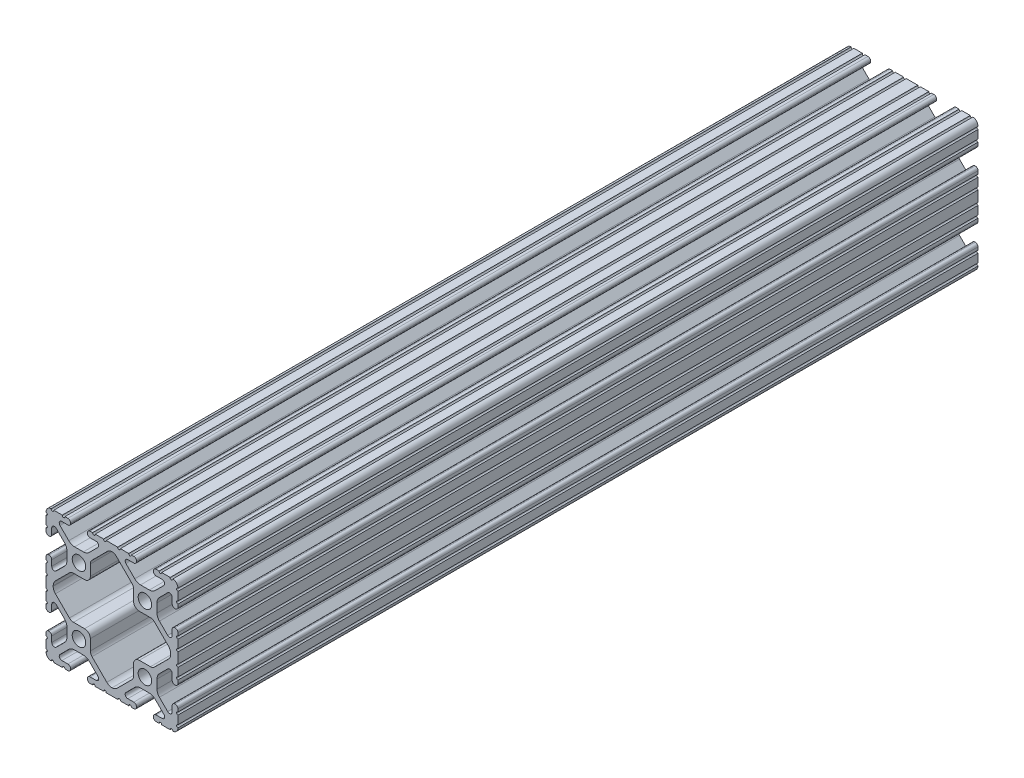
SolidWorks part; units mm, degrees
material "6061 Alloy"
ref_plane "Front Plane" through (0, 0, 0) normal (0, 0, 1) x (1, 0, 0)
ref_plane "Top Plane" through (0, 0, 0) normal (0, 1, 0) x (1, 0, 0)
ref_plane "Right Plane" through (0, 0, 0) normal (1, 0, 0) x (0, 0, -1)
sketch "Sketch1" plane through (0, 0, 0) normal (0, 0, 1) x (1, 0, 0)
  line L1 (-2.2101, -25.4) -> (2.2101, -25.4)
  line L2 (12.7883, 29.5847) -> (12.7883, -24.0404) construction
  line L3 (7.4579, -25.4) -> (8.4051, -25.4)
  line L4 (9.4615, -24.3587) -> (9.4615, -24.2315)
  line L5 (6.0878, -23.1902) -> (8.4051, -23.1902)
  line L6 (-12.7, -45.1098) -> (-12.7, 28.7522) construction
  line L7 (-25.8162, -12.7) -> (-12.7, -12.7) construction
  line L8 (0, 25.5922) -> (0, -25.5922) construction
  line L9 (-22.8238, 0) -> (0, 0) construction
  line L10 (8.763, -18.1257) -> (5.388, -21.5008)
  line L11 (14.3919, -17.1958) -> (11.0081, -17.1958)
  line L12 (20.012, -21.5008) -> (16.637, -18.1257)
  line L13 (16.9799, -23.1901) -> (19.2977, -23.1901)
  line L14 (15.9385, -24.3585) -> (15.9385, -24.2315)
  line L15 (16.9949, -25.4) -> (18.134, -25.4)
  line L16 (19.1384, -25.4) -> (20.1295, -25.4)
  line L17 (20.1295, -25.4) -> (22.4132, -25.4)
  line L18 (23.4501, -25.4) -> (23.4176, -25.4)
  line L19 (25.4, -23.294) -> (25.4, -23.2686)
  line L20 (25.4, -22.2526) -> (25.4, -21.1604)
  line L21 (25.4, -21.1604) -> (25.4, -19.0252)
  line L22 (25.4, -18.0092) -> (25.4, -16.916)
  line L23 (24.2316, -15.8746) -> (24.3586, -15.8746)
  line L24 (23.1902, -19.101) -> (23.1902, -16.916)
  line L25 (18.2781, -16.6418) -> (21.4558, -19.8194)
  line L26 (17.3482, -11.0035) -> (17.3482, -14.3967)
  line L27 (21.4566, -5.5875) -> (18.2808, -8.7557)
  line L28 (23.1902, -8.484) -> (23.1902, -6.3068)
  line L29 (-1.9878, -21.7759) -> (-7.684, -16.0797)
  line L30 (10.541, 8.1792) -> (14.8161, 8.1792)
  line L31 (-16.3772, -7.5334) -> (-21.7734, -2.1502)
  line L32 (24.3586, -9.5254) -> (24.2316, -9.5254)
  line L33 (25.4, -8.484) -> (25.4, -7.3277)
  line L34 (25.4, -3.0843) -> (25.4, -6.3117)
  line L35 (-25.4, 6.3117) -> (-25.4, 3.0843)
  line L36 (-22.6314, 0.0822) -> (-22.6314, -0.0822)
  line L37 (16.3772, -7.5334) -> (21.7734, -2.1502)
  line L38 (-14.8165, -8.1788) -> (-10.541, -8.1788)
  line L39 (12.7, -12.7) -> (25.8162, -12.7) construction
  line L40 (1.9878, -21.7759) -> (7.684, -16.0797)
  line L41 (3.2145, -25.4) -> (6.4535, -25.4)
  line L42 (22.6314, 0.0822) -> (22.6314, -0.0822)
  line L43 (-17.3482, -11.0035) -> (-17.3482, -14.3967)
  line L44 (25.4, 6.3117) -> (25.4, 3.0843)
  line L45 (-23.4501, -25.4) -> (-23.4176, -25.4)
  line L46 (-5.2705, 25.4) -> (-3.2145, 25.4)
  line L47 (-6.4535, 25.4) -> (-5.2705, 25.4)
  line L48 (-8.4051, 25.4) -> (-7.4579, 25.4)
  line L49 (-9.4615, 24.2315) -> (-9.4615, 24.3587)
  line L50 (-8.4051, 23.1902) -> (-6.0878, 23.1902)
  line L51 (-8.763, 18.1257) -> (-5.388, 21.5008)
  line L52 (-14.3919, 17.1958) -> (-11.0081, 17.1958)
  line L53 (-20.012, 21.5008) -> (-16.637, 18.1257)
  line L54 (-19.2977, 23.1901) -> (-16.9799, 23.1901)
  line L55 (-15.9385, 24.3585) -> (-15.9385, 24.2315)
  line L56 (-18.134, 25.4) -> (-16.9949, 25.4)
  line L57 (-20.1295, 25.4) -> (-19.1384, 25.4)
  line L58 (-22.4132, 25.4) -> (-20.1295, 25.4)
  line L59 (-23.4501, 25.4) -> (-23.4176, 25.4)
  line L60 (-25.4, 23.2686) -> (-25.4, 23.294)
  line L61 (-25.4, 21.1604) -> (-25.4, 22.2526)
  line L62 (-25.4, 19.0252) -> (-25.4, 21.1604)
  line L63 (-25.4, 16.916) -> (-25.4, 18.0092)
  line L64 (-24.3586, 15.8746) -> (-24.2316, 15.8746)
  line L65 (-23.1902, 19.101) -> (-23.1902, 16.916)
  line L66 (-18.2781, 16.6418) -> (-21.4558, 19.8194)
  line L67 (-17.3482, 11.0035) -> (-17.3482, 14.3967)
  line L68 (-21.4566, 5.5875) -> (-18.2808, 8.7557)
  line L69 (-23.1902, 6.3068) -> (-23.1902, 8.484)
  line L70 (-24.3586, 9.5254) -> (-24.2316, 9.5254)
  line L71 (-25.4, 7.3277) -> (-25.4, 8.484)
  line L74 (-14.8165, 8.1788) -> (-10.541, 8.1788)
  line L75 (-8.3312, 10.3886) -> (-8.3312, 14.5171)
  line L76 (3.2145, 25.4) -> (6.4535, 25.4)
  line L77 (1.7956, 21.9681) -> (7.684, 16.0797)
  line L78 (12.7, 12.7) -> (25.8162, 12.7) construction
  line L80 (16.3768, 7.5339) -> (21.7734, 2.1502)
  line L82 (25.4, 2.0683) -> (25.4, -2.0683)
  line L83 (8.3312, 12.7001) -> (8.3312, 10.389)
  line L84 (25.4, 7.3277) -> (25.4, 8.484)
  line L85 (24.3586, 9.5254) -> (24.2316, 9.5254)
  line L86 (-16.3772, 7.5334) -> (-21.7734, 2.1502)
  line L88 (-1.7956, 21.9681) -> (-7.684, 16.0797)
  line L89 (23.1902, 6.3068) -> (23.1902, 8.484)
  line L90 (21.4566, 5.5875) -> (18.2808, 8.7557)
  line L91 (17.3482, 11.0035) -> (17.3482, 14.3967)
  line L92 (18.2781, 16.6418) -> (21.4558, 19.8194)
  line L93 (23.1902, 19.101) -> (23.1902, 16.916)
  line L94 (24.2316, 15.8746) -> (24.3586, 15.8746)
  line L95 (25.4, 16.916) -> (25.4, 18.0092)
  line L96 (25.4, 19.0252) -> (25.4, 21.1604)
  line L97 (25.4, 21.1604) -> (25.4, 22.2526)
  line L98 (25.4, 23.2686) -> (25.4, 23.294)
  line L99 (23.4501, 25.4) -> (23.4176, 25.4)
  line L100 (20.1295, 25.4) -> (22.4132, 25.4)
  line L101 (19.1384, 25.4) -> (20.1295, 25.4)
  line L102 (16.9949, 25.4) -> (18.134, 25.4)
  line L103 (15.9385, 24.3585) -> (15.9385, 24.2315)
  line L104 (16.9799, 23.1901) -> (19.2977, 23.1901)
  line L105 (20.012, 21.5008) -> (16.637, 18.1257)
  line L106 (14.3919, 17.1958) -> (11.0081, 17.1958)
  line L107 (8.763, 18.1257) -> (5.388, 21.5008)
  line L108 (-25.8162, 12.7) -> (-12.7, 12.7) construction
  line L109 (6.0878, 23.1902) -> (8.4051, 23.1902)
  line L110 (9.4615, 24.2315) -> (9.4615, 24.3587)
  line L111 (7.4579, 25.4) -> (8.4051, 25.4)
  line L112 (8.3312, 12.7001) -> (8.3312, 14.5171)
  line L113 (-2.2101, 25.4) -> (2.2101, 25.4)
  line L114 (-22.4132, -25.4) -> (-20.1295, -25.4)
  line L115 (-20.1295, -25.4) -> (-19.1384, -25.4)
  line L116 (-18.134, -25.4) -> (-16.9949, -25.4)
  line L117 (-8.4051, -25.4) -> (-7.4579, -25.4)
  line L118 (-6.4535, -25.4) -> (-5.2705, -25.4)
  line L119 (-5.2705, -25.4) -> (-3.2145, -25.4)
  line L120 (-19.2977, -23.1901) -> (-16.9799, -23.1901)
  line L121 (-8.4051, -23.1902) -> (-6.0878, -23.1902)
  line L122 (-8.3312, -14.5171) -> (-8.3312, -10.3886)
  line L123 (-14.3919, -17.1958) -> (-11.0081, -17.1958)
  line L125 (-24.3586, -15.8746) -> (-24.2316, -15.8746)
  line L127 (-24.3586, -9.5254) -> (-24.2316, -9.5254)
  line L128 (14.8165, -8.1788) -> (10.541, -8.1788)
  line L129 (8.3312, -10.3886) -> (8.3312, -14.5171)
  line L130 (-9.4615, -24.3587) -> (-9.4615, -24.2315)
  line L132 (-15.9385, -24.3585) -> (-15.9385, -24.2315)
  line L134 (-25.4, -23.294) -> (-25.4, -23.2686)
  line L135 (-25.4, -22.2526) -> (-25.4, -21.1604)
  line L136 (-25.4, -21.1604) -> (-25.4, -19.0252)
  line L137 (-25.4, -18.0092) -> (-25.4, -16.916)
  line L138 (-25.4, -8.484) -> (-25.4, -7.3277)
  line L139 (-25.4, -6.3117) -> (-25.4, -4.1765)
  line L140 (-25.4, -4.1765) -> (-25.4, -3.0843)
  line L141 (-25.4, -2.0683) -> (-25.4, 2.0683)
  line L143 (-23.1902, -19.101) -> (-23.1902, -16.916)
  line L144 (-23.1902, -8.484) -> (-23.1902, -6.3068)
  line L198 (-21.4566, -5.5875) -> (-18.2808, -8.7557)
  line L200 (-18.2781, -16.6418) -> (-21.4558, -19.8194)
  line L213 (-20.012, -21.5008) -> (-16.637, -18.1257)
  line L215 (-8.763, -18.1257) -> (-5.388, -21.5008)
  arc A0 (6.4535, -25.4) -> (7.4579, -25.4) centre (6.9557, -25.3234) cw
  arc A1 (9.4615, -24.3587) -> (8.4051, -25.4) centre (8.4201, -24.3587) cw
  arc A2 (8.4051, -23.1902) -> (9.4615, -24.2315) centre (8.4201, -24.2315) cw
  arc A3 (6.0878, -23.1902) -> (5.388, -21.5008) centre (6.0878, -22.2006) cw
  arc A4 (8.763, -18.1257) -> (11.0081, -17.1958) centre (11.0081, -20.3708) cw
  arc A5 (14.3919, -17.1958) -> (16.637, -18.1257) centre (14.3919, -20.3708) cw
  arc A6 (20.012, -21.5008) -> (19.2977, -23.1901) centre (19.3122, -22.2006) cw
  arc A7 (15.9385, -24.2315) -> (16.9799, -23.1901) centre (16.9799, -24.2315) cw
  arc A8 (16.9949, -25.4) -> (15.9385, -24.3585) centre (16.9799, -24.3587) cw
  arc A9 (18.134, -25.4) -> (19.1384, -25.4) centre (18.6362, -25.3234) cw
  arc A10 (22.4132, -25.4) -> (23.4176, -25.4) centre (22.9154, -25.3234) cw
  arc A11 (25.4, -23.294) -> (23.4501, -25.4) centre (23.2918, -23.2977) cw
  arc A12 (25.4, -23.2686) -> (25.4, -22.2526) centre (25.4, -22.7606) cw
  arc A13 (25.4, -19.0252) -> (25.4, -18.0092) centre (25.4, -18.5172) cw
  arc A14 (24.3586, -15.8746) -> (25.4, -16.916) centre (24.3586, -16.916) cw
  arc A15 (23.1902, -16.916) -> (24.2316, -15.8746) centre (24.2316, -16.916) cw
  arc A16 (23.1902, -19.101) -> (21.4558, -19.8194) centre (22.1742, -19.101) cw
  arc A17 (18.2781, -16.6418) -> (17.3482, -14.3967) centre (20.5232, -14.3967) cw
  arc A18 (17.3482, -11.0035) -> (18.2808, -8.7557) centre (20.5232, -11.0035) cw
  arc A19 (0, -22.6304) -> (-1.9878, -21.7759) centre (0.0777, -19.7104) cw
  arc A20 (21.4566, -5.5875) -> (23.1902, -6.3068) centre (22.1742, -6.3068) cw
  arc A21 (24.2316, -9.5254) -> (23.1902, -8.484) centre (24.2316, -8.484) cw
  arc A22 (-14.8165, -8.1788) -> (-16.3772, -7.5334) centre (-14.8165, -5.969) cw
  arc A23 (-8.3312, -10.3886) -> (-10.541, -8.1788) centre (-10.541, -10.3886) ccw
  arc A24 (25.4, -8.484) -> (24.3586, -9.5254) centre (24.3586, -8.484) cw
  arc A25 (25.4, -7.3277) -> (25.4, -6.3117) centre (25.4, -6.8197) cw
  arc A26 (-22.6314, 0.0822) -> (-21.7734, 2.1502) centre (-19.7104, 0.0822) cw
  arc A27 (-7.684, -16.0797) -> (-8.3312, -14.5171) centre (-6.1214, -14.5171) cw
  arc A28 (-8.3312, 10.3886) -> (-10.541, 8.1788) centre (-10.541, 10.3886) cw
  circle A29 centre (12.7, -12.7) radius 2.6035
  arc A30 (14.8165, -8.1788) -> (16.3772, -7.5334) centre (14.8165, -5.969) ccw
  arc A31 (8.3312, -10.3886) -> (10.541, -8.1788) centre (10.541, -10.3886) cw
  arc A32 (8.3312, -14.5171) -> (7.684, -16.0797) centre (6.1214, -14.5171) cw
  arc A33 (0, -22.6304) -> (1.9878, -21.7759) centre (-0.0777, -19.7104) ccw
  arc A34 (2.2101, -25.4) -> (3.2145, -25.4) centre (2.7123, -25.3234) cw
  arc A35 (25.4, -3.0843) -> (25.4, -2.0683) centre (25.4, -2.5763) cw
  arc A36 (22.6314, 0.0822) -> (21.7734, 2.1502) centre (19.7104, 0.0822) ccw
  circle A37 centre (-12.7, -12.7) radius 2.6035
  arc A38 (-2.2101, 25.4) -> (-3.2145, 25.4) centre (-2.7123, 25.3234) cw
  arc A39 (-6.4535, 25.4) -> (-7.4579, 25.4) centre (-6.9557, 25.3234) cw
  arc A40 (-9.4615, 24.3587) -> (-8.4051, 25.4) centre (-8.4201, 24.3587) cw
  arc A41 (-8.4051, 23.1902) -> (-9.4615, 24.2315) centre (-8.4201, 24.2315) cw
  arc A42 (-6.0878, 23.1902) -> (-5.388, 21.5008) centre (-6.0878, 22.2006) cw
  arc A43 (-8.763, 18.1257) -> (-11.0081, 17.1958) centre (-11.0081, 20.3708) cw
  arc A44 (-14.3919, 17.1958) -> (-16.637, 18.1257) centre (-14.3919, 20.3708) cw
  arc A45 (-20.012, 21.5008) -> (-19.2977, 23.1901) centre (-19.3122, 22.2006) cw
  arc A46 (-15.9385, 24.2315) -> (-16.9799, 23.1901) centre (-16.9799, 24.2315) cw
  arc A47 (-16.9949, 25.4) -> (-15.9385, 24.3585) centre (-16.9799, 24.3587) cw
  arc A48 (-18.134, 25.4) -> (-19.1384, 25.4) centre (-18.6362, 25.3234) cw
  arc A49 (-22.4132, 25.4) -> (-23.4176, 25.4) centre (-22.9154, 25.3234) cw
  arc A50 (-25.4, 23.294) -> (-23.4501, 25.4) centre (-23.2918, 23.2977) cw
  arc A51 (-25.4, 23.2686) -> (-25.4, 22.2526) centre (-25.4, 22.7606) cw
  arc A52 (-25.4, 19.0252) -> (-25.4, 18.0092) centre (-25.4, 18.5172) cw
  arc A53 (-24.3586, 15.8746) -> (-25.4, 16.916) centre (-24.3586, 16.916) cw
  arc A54 (-23.1902, 16.916) -> (-24.2316, 15.8746) centre (-24.2316, 16.916) cw
  arc A55 (-23.1902, 19.101) -> (-21.4558, 19.8194) centre (-22.1742, 19.101) cw
  arc A56 (-18.2781, 16.6418) -> (-17.3482, 14.3967) centre (-20.5232, 14.3967) cw
  arc A57 (-17.3482, 11.0035) -> (-18.2808, 8.7557) centre (-20.5232, 11.0035) cw
  arc A58 (-21.4566, 5.5875) -> (-23.1902, 6.3068) centre (-22.1742, 6.3068) cw
  arc A59 (-24.2316, 9.5254) -> (-23.1902, 8.484) centre (-24.2316, 8.484) cw
  arc A60 (-25.4, 8.484) -> (-24.3586, 9.5254) centre (-24.3586, 8.484) cw
  arc A61 (-25.4, 7.3277) -> (-25.4, 6.3117) centre (-25.4, 6.8197) cw
  arc A62 (-25.4, 3.0843) -> (-25.4, 2.0683) centre (-25.4, 2.5763) cw
  circle A63 centre (-12.7, 12.7) radius 2.6035
  arc A64 (-8.3312, 14.5171) -> (-7.684, 16.0797) centre (-6.1214, 14.5171) cw
  arc A65 (2.2101, 25.4) -> (3.2145, 25.4) centre (2.7123, 25.3234) ccw
  arc A66 (0, 22.8111) -> (-1.7956, 21.9681) centre (0.2699, 19.9026) ccw
  arc A67 (8.3312, 14.5171) -> (7.684, 16.0797) centre (6.1214, 14.5171) ccw
  arc A68 (10.541, 8.1792) -> (8.3312, 10.389) centre (10.541, 10.389) cw
  arc A69 (14.8161, 8.1792) -> (16.3768, 7.5339) centre (14.8161, 5.9694) cw
  circle A70 centre (12.7, 12.7) radius 2.6035
  arc A71 (25.4, 3.0843) -> (25.4, 2.0683) centre (25.4, 2.5763) ccw
  arc A72 (-14.8165, 8.1788) -> (-16.3772, 7.5334) centre (-14.8165, 5.969) ccw
  arc A73 (25.4, 7.3277) -> (25.4, 6.3117) centre (25.4, 6.8197) ccw
  arc A74 (25.4, 8.484) -> (24.3586, 9.5254) centre (24.3586, 8.484) ccw
  arc A75 (22.6314, -0.0822) -> (21.7734, -2.1502) centre (19.7104, -0.0822) cw
  arc A76 (-22.6314, -0.0822) -> (-21.7734, -2.1502) centre (-19.7104, -0.0822) ccw
  arc A77 (24.2316, 9.5254) -> (23.1902, 8.484) centre (24.2316, 8.484) ccw
  arc A78 (21.4566, 5.5875) -> (23.1902, 6.3068) centre (22.1742, 6.3068) ccw
  arc A79 (1.7956, 21.9681) -> (0, 22.8111) centre (-0.2699, 19.9026) ccw
  arc A80 (17.3482, 11.0035) -> (18.2808, 8.7557) centre (20.5232, 11.0035) ccw
  arc A81 (18.2781, 16.6418) -> (17.3482, 14.3967) centre (20.5232, 14.3967) ccw
  arc A82 (23.1902, 19.101) -> (21.4558, 19.8194) centre (22.1742, 19.101) ccw
  arc A83 (23.1902, 16.916) -> (24.2316, 15.8746) centre (24.2316, 16.916) ccw
  arc A84 (24.3586, 15.8746) -> (25.4, 16.916) centre (24.3586, 16.916) ccw
  arc A85 (25.4, 19.0252) -> (25.4, 18.0092) centre (25.4, 18.5172) ccw
  arc A86 (25.4, 23.2686) -> (25.4, 22.2526) centre (25.4, 22.7606) ccw
  arc A87 (25.4, 23.294) -> (23.4501, 25.4) centre (23.2918, 23.2977) ccw
  arc A88 (22.4132, 25.4) -> (23.4176, 25.4) centre (22.9154, 25.3234) ccw
  arc A89 (18.134, 25.4) -> (19.1384, 25.4) centre (18.6362, 25.3234) ccw
  arc A90 (16.9949, 25.4) -> (15.9385, 24.3585) centre (16.9799, 24.3587) ccw
  arc A91 (15.9385, 24.2315) -> (16.9799, 23.1901) centre (16.9799, 24.2315) ccw
  arc A92 (20.012, 21.5008) -> (19.2977, 23.1901) centre (19.3122, 22.2006) ccw
  arc A93 (14.3919, 17.1958) -> (16.637, 18.1257) centre (14.3919, 20.3708) ccw
  arc A94 (8.763, 18.1257) -> (11.0081, 17.1958) centre (11.0081, 20.3708) ccw
  arc A95 (6.0878, 23.1902) -> (5.388, 21.5008) centre (6.0878, 22.2006) ccw
  arc A96 (8.4051, 23.1902) -> (9.4615, 24.2315) centre (8.4201, 24.2315) ccw
  arc A97 (9.4615, 24.3587) -> (8.4051, 25.4) centre (8.4201, 24.3587) ccw
  arc A98 (6.4535, 25.4) -> (7.4579, 25.4) centre (6.9557, 25.3234) ccw
  arc A182 (-25.4, -3.0843) -> (-25.4, -2.0683) centre (-25.4, -2.5763) ccw
  arc A183 (-25.4, -7.3277) -> (-25.4, -6.3117) centre (-25.4, -6.8197) ccw
  arc A184 (-25.4, -8.484) -> (-24.3586, -9.5254) centre (-24.3586, -8.484) ccw
  arc A185 (-24.2316, -9.5254) -> (-23.1902, -8.484) centre (-24.2316, -8.484) ccw
  arc A186 (-21.4566, -5.5875) -> (-23.1902, -6.3068) centre (-22.1742, -6.3068) ccw
  arc A187 (-17.3482, -11.0035) -> (-18.2808, -8.7557) centre (-20.5232, -11.0035) ccw
  arc A188 (-18.2781, -16.6418) -> (-17.3482, -14.3967) centre (-20.5232, -14.3967) ccw
  arc A189 (-23.1902, -19.101) -> (-21.4558, -19.8194) centre (-22.1742, -19.101) ccw
  arc A190 (-23.1902, -16.916) -> (-24.2316, -15.8746) centre (-24.2316, -16.916) ccw
  arc A191 (-24.3586, -15.8746) -> (-25.4, -16.916) centre (-24.3586, -16.916) ccw
  arc A192 (-25.4, -19.0252) -> (-25.4, -18.0092) centre (-25.4, -18.5172) ccw
  arc A193 (-25.4, -23.2686) -> (-25.4, -22.2526) centre (-25.4, -22.7606) ccw
  arc A194 (-25.4, -23.294) -> (-23.4501, -25.4) centre (-23.2918, -23.2977) ccw
  arc A195 (-22.4132, -25.4) -> (-23.4176, -25.4) centre (-22.9154, -25.3234) ccw
  arc A196 (-18.134, -25.4) -> (-19.1384, -25.4) centre (-18.6362, -25.3234) ccw
  arc A197 (-16.9949, -25.4) -> (-15.9385, -24.3585) centre (-16.9799, -24.3587) ccw
  arc A198 (-15.9385, -24.2315) -> (-16.9799, -23.1901) centre (-16.9799, -24.2315) ccw
  arc A199 (-20.012, -21.5008) -> (-19.2977, -23.1901) centre (-19.3122, -22.2006) ccw
  arc A200 (-14.3919, -17.1958) -> (-16.637, -18.1257) centre (-14.3919, -20.3708) ccw
  arc A201 (-8.763, -18.1257) -> (-11.0081, -17.1958) centre (-11.0081, -20.3708) ccw
  arc A202 (-6.0878, -23.1902) -> (-5.388, -21.5008) centre (-6.0878, -22.2006) ccw
  arc A203 (-8.4051, -23.1902) -> (-9.4615, -24.2315) centre (-8.4201, -24.2315) ccw
  arc A204 (-9.4615, -24.3587) -> (-8.4051, -25.4) centre (-8.4201, -24.3587) ccw
  arc A205 (-6.4535, -25.4) -> (-7.4579, -25.4) centre (-6.9557, -25.3234) ccw
  arc A206 (-2.2101, -25.4) -> (-3.2145, -25.4) centre (-2.7123, -25.3234) ccw
  point P397 (16.6343, 7.277)
  dimension "D1" = 5.207
  dimension "D3" = 6.477
  dimension "D4" = 8.2042
  dimension "D5" = 25.4
  dimension "D10" = 12.7
  dimension "D8" = 2.2098
  dimension "D9" = 2.2098
  dimension "D12" = 2.2098
  dimension "D13" = 2.2098
  dimension "D14" = 2.2098
  dimension "D15" = 2.2098
  dimension "D16" = 2.921
  dimension "D17" = 2.921
  dimension "D18" = 2.921
  dimension "D19" = 2.921
  dimension "D20" = 2.921
  dimension "D21" = 2.921
  dimension "D2" = 2.2098
  dimension "D6" = 14.859
  dimension "D7" = 50.8
  dimension "D11" = 2.2098
extrude "Extrude1" add sketch "Sketch1" against normal blind 308.102
